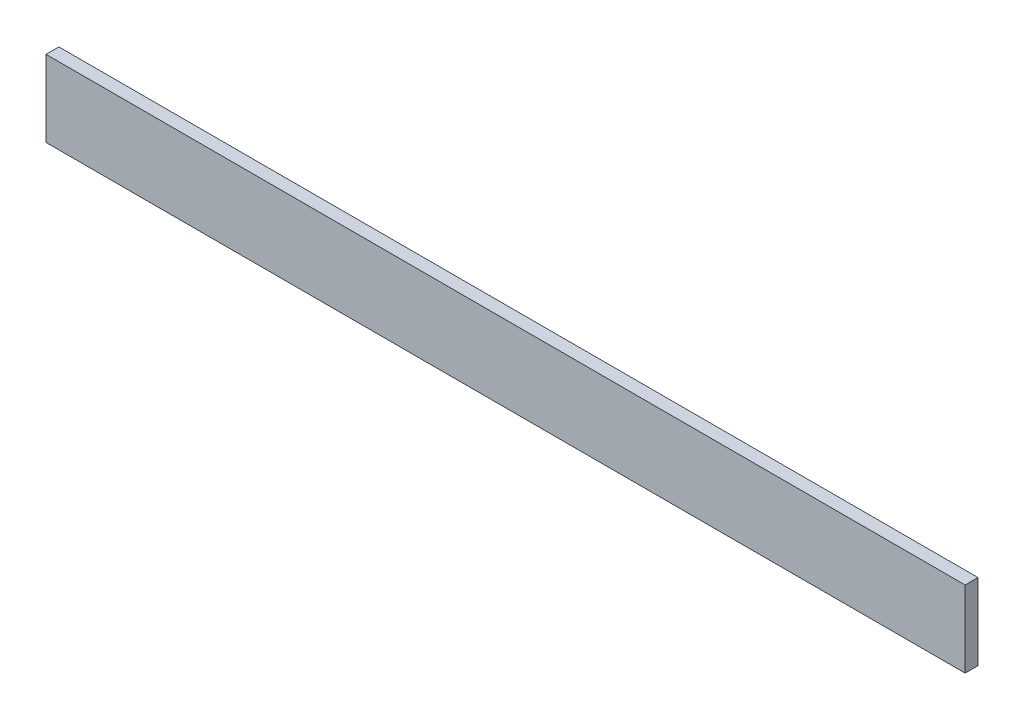
SolidWorks part; units mm, degrees
ref_plane "Front Plane" through (0, 0, 0) normal (0, 0, 1) x (1, 0, 0)
ref_plane "Top Plane" through (0, 0, 0) normal (0, 1, 0) x (1, 0, 0)
ref_plane "Right Plane" through (0, 0, 0) normal (1, 0, 0) x (0, 0, -1)
sketch "Sketch1" plane through (0, 0, 0) normal (0, 0, 1) x (1, 0, 0)
  line L1 (-107.061, 8.89) -> (107.061, 8.89)
  line L2 (-107.061, 8.89) -> (-107.061, -8.89)
  line L3 (-107.061, -8.89) -> (107.061, -8.89)
  line L4 (107.061, 8.89) -> (107.061, -8.89)
  line L5 (-107.061, 8.89) -> (107.061, -8.89) construction
  line L6 (-107.061, -8.89) -> (107.061, 8.89) construction
  point P0 (0, 0)
  dimension "D1" = 17.78
  dimension "D2" = 214.122
extrude "Boss-Extrude1" add sketch "Sketch1" along normal blind 3
